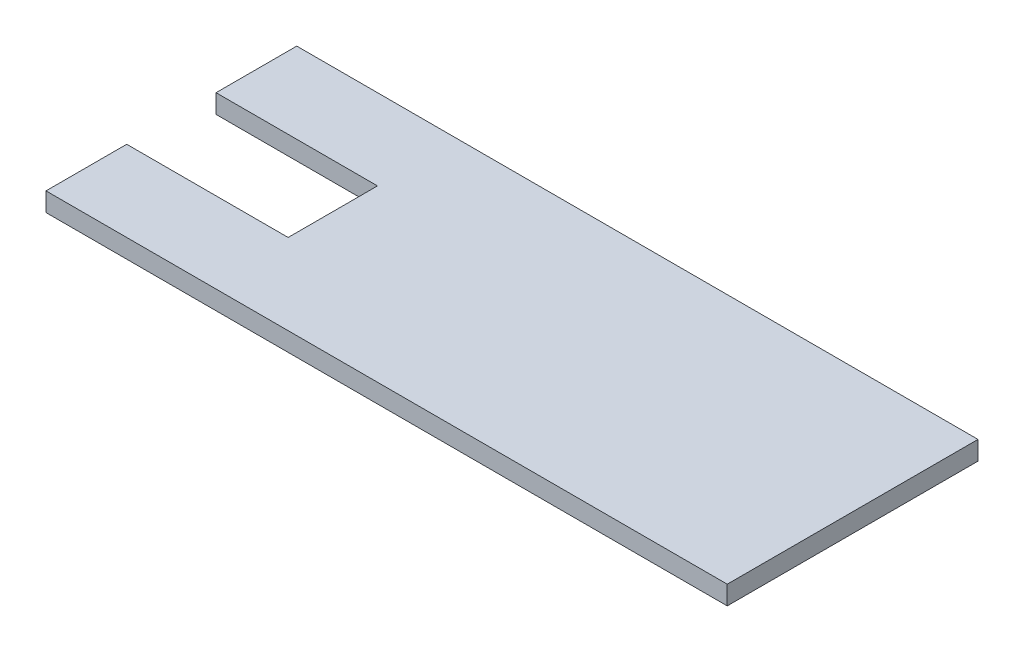
SolidWorks part; units mm, degrees
ref_plane "Front Plane" through (0, 0, 0) normal (0, 0, 1) x (1, 0, 0)
ref_plane "Top Plane" through (0, 0, 0) normal (0, 1, 0) x (1, 0, 0)
ref_plane "Right Plane" through (0, 0, 0) normal (1, 0, 0) x (0, 0, -1)
sketch "Sketch2" plane through (0, 0, 0) normal (0, 1, 0) x (1, 0, 0)
  line L0 (-63.3, 23.3) -> (63.3, 23.3)
  line L1 (-63.3, 23.3) -> (-63.3, -23.3)
  line L2 (-63.3, -23.3) -> (63.3, -23.3)
  line L3 (63.3, 23.3) -> (63.3, -23.3)
extrude "Boss-Extrude1" add sketch "Sketch2" along normal blind 3.5
sketch "Sketch3" plane through (0, 3.5, 0) normal (0, 1, 0) x (1, 0, 0)
  line L0 (-63.3, 23.3) -> (-63.3, -23.3) construction
  line L1 (-63.3, 8.3) -> (-33.3, 8.3)
  line L2 (-63.3, 8.3) -> (-63.3, -8.3)
  line L3 (-63.3, -8.3) -> (-33.3, -8.3)
  line L4 (-33.3, 8.3) -> (-33.3, -8.3)
  line L5 (63.3, 23.3) -> (-63.3, 23.3) construction
  line L6 (-63.3, -23.3) -> (63.3, -23.3) construction
  dimension "D1" = 15
  dimension "D2" = 15
  dimension "D3" = 30
extrude "Cut-Extrude1" cut sketch "Sketch3" against normal blind 3.5
